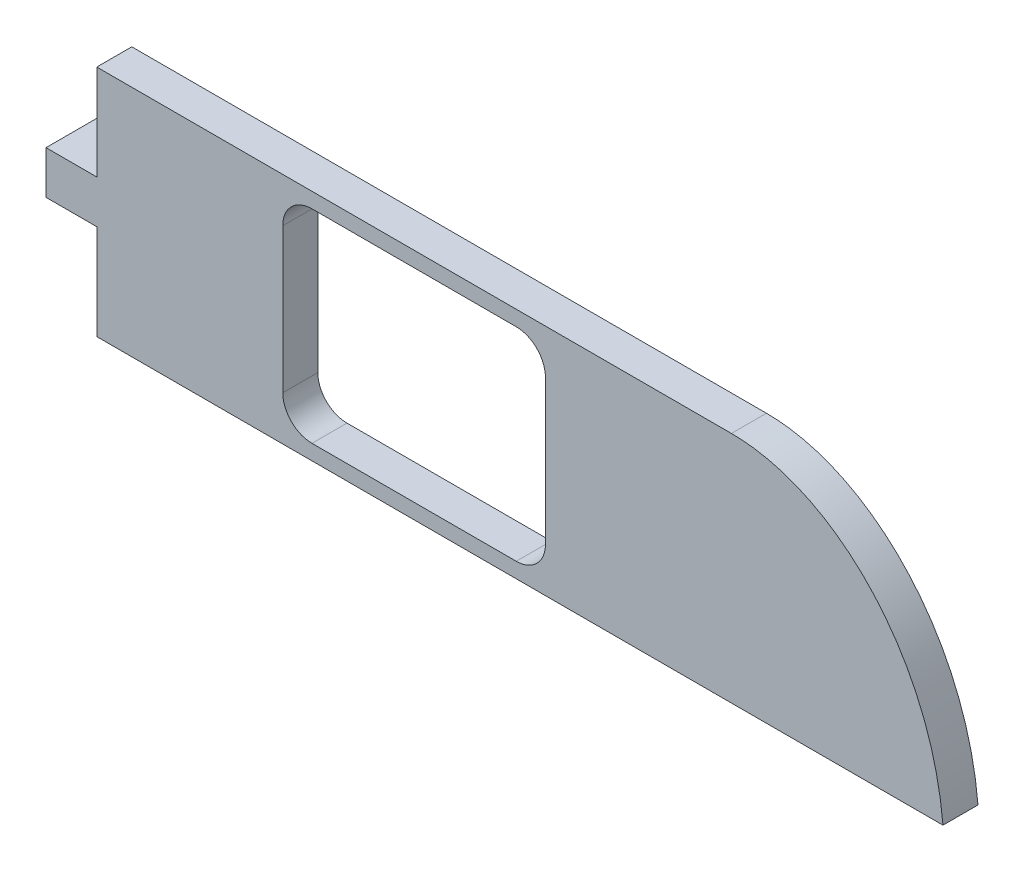
SolidWorks part; units mm, degrees
ref_plane "Alzado" through (0, 0, 0) normal (0, 0, 1) x (1, 0, 0)
ref_plane "Planta" through (0, 0, 0) normal (0, 1, 0) x (1, 0, 0)
ref_plane "Vista lateral" through (0, 0, 0) normal (1, 0, 0) x (0, 0, -1)
sketch "Croquis1" plane through (0, 0, 0) normal (0, 0, 1) x (1, 0, 0)
  line L0 (-80.4587, -26.4093) -> (-69.5862, -26.4093)
  line L1 (-80.4587, -26.4093) -> (-80.4587, -28.0402)
  line L2 (-69.5862, -30.4093) -> (-80.4587, -30.4093)
  line L3 (-80.4587, -28.0402) -> (-81.3285, -28.0402)
  line L4 (-69.5862, -30.4093) -> (-65.9619, -30.4093)
  line L5 (-72.7724, -26.6697) -> (-77.2724, -26.6697)
  line L6 (-80.4587, -28.7784) -> (-80.4587, -30.4093)
  line L7 (-81.3285, -28.0402) -> (-81.3285, -28.7784)
  line L8 (-81.3285, -28.7784) -> (-80.4587, -28.7784)
  line L9 (-72.7724, -30.1489) -> (-77.2724, -30.1489)
  line L10 (-77.2724, -26.6697) -> (-77.2724, -30.1489)
  line L11 (-72.7724, -26.6697) -> (-72.7724, -30.1489)
  spline S0 degree 3 poles (-69.5862, -26.4093) (-67.8253, -26.4093) (-66.1716, -28.0638) (-65.9619, -30.4093) knots 0 0 0 0 1 1 1 1
  point P14 (-75.0224, -26.6697)
  point P17 (-75.0224, -30.1489)
  dimension "D2" = 4
extrude "Saliente-Extruir1" add sketch "Croquis1" along normal blind 0.6
fillet "Redondeo1" radius 0.5 4 edges at (-72.7724, -30.1489, 0.3) (-72.7724, -26.6697, 0.3) (-77.2724, -26.6697, 0.3) (-77.2724, -30.1489, 0.3)
sketch "Croquis2" plane through (0, 0, 0) normal (0, 0, -1) x (-1, 0, 0)
  line L0 (81.3285, -28.0402) -> (81.0285, -28.0402)
  line L1 (80.4587, -28.0402) -> (81.3285, -28.0402) construction
  line L2 (81.0285, -28.0402) -> (81.0285, -28.7784)
  line L3 (81.3285, -28.7784) -> (80.4587, -28.7784) construction
  line L4 (81.0285, -28.7784) -> (81.3285, -28.7784)
  line L5 (81.3285, -28.7784) -> (81.3285, -28.0402)
extrude "Saliente-Extruir2" add sketch "Croquis2" along normal blind 0.8
